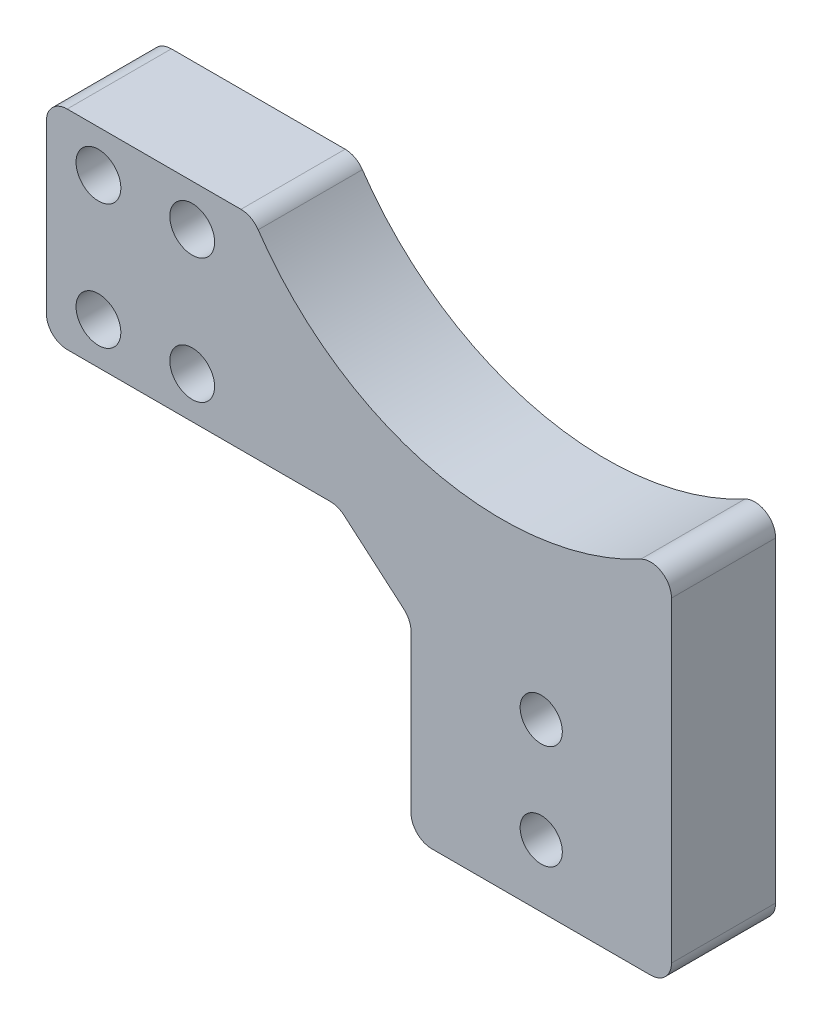
SolidWorks part; units mm, degrees
material "ABS"
ref_plane "前视基准面" through (0, 0, 0) normal (0, 0, 1) x (1, 0, 0)
ref_plane "上视基准面" through (0, 0, 0) normal (0, 1, 0) x (1, 0, 0)
ref_plane "右视基准面" through (0, 0, 0) normal (1, 0, 0) x (0, 0, -1)
other "Configuration Table"
sketch "草图1" plane through (0, 0, 0) normal (0, 0, 1) x (1, 0, 0)
  line L0 (0, 0) -> (0, -24)
  line L1 (0, -24) -> (25, -24)
  line L2 (25, -24) -> (25, 17.9268)
  line L3 (-15.2387, 26) -> (-35, 26)
  line L4 (-35, 26) -> (-35, 6)
  line L5 (-35, 6) -> (-7, 6)
  line L6 (-7, 6) -> (0, 0)
  arc A0 (25, 17.9268) -> (-15.2387, 26) centre (8.7, 41) cw
  dimension "D3" = 28.25
  dimension "D1" = 6
  dimension "D2" = 7
  dimension "D4" = 25
  dimension "D5" = 20
  dimension "D6" = 16.3
  dimension "D7" = 35
  dimension "D8" = 60
  dimension "D9" = 50
extrude "凸台-拉伸1" add sketch "草图1" along normal mid plane 10
fillet "圆角1" radius 2 6 edges at (-7, 6, 0) (-35, 6, 0) (25, -24, 0) (0, -24, 0) (0, 0, 0) (-35, 26, 0)
fillet "圆角2" radius 2 2 edges at (25, 17.9268, 0) (-15.2387, 26, 0)
sketch "草图2" plane through (0, 0, 5) normal (0, 0, 1) x (1, 0, 0)
  line L0 (-33, 6) -> (-7.7398, 6) construction
  line L1 (7.5, -12) -> (17.5, -12) construction
  line L2 (7.5, -12) -> (7.5, -2) construction
  line L3 (7.5, -2) -> (17.5, -2) construction
  line L4 (17.5, -12) -> (17.5, -2) construction
  line L5 (7.5, -12) -> (17.5, -2) construction
  line L6 (7.5, -2) -> (17.5, -12) construction
  line L7 (12.5, -7) -> (12.5, -24) construction
  line L8 (2, -24) -> (23, -24) construction
  circle A4 centre (12.5, -2) radius 2.025
  circle A5 centre (12.5, -12) radius 2.025
  point P0 (12.5, -7)
  dimension "D4" = 4.05
  dimension "D1" = 8
  dimension "D2" = 10
  dimension "D3" = 10
extrude "切除-拉伸1" cut sketch "草图2" against normal through all
sketch "草图3" plane through (0, 0, 5) normal (0, 0, 1) x (1, 0, 0)
  line L0 (0, -0.9199) -> (0, -22) construction
  line L1 (0, -18) -> (25, -18)
  line L2 (0, -18) -> (0, -24)
  line L3 (0, -24) -> (25, -24)
  line L4 (25, -18) -> (25, -24)
  line L5 (2, -24) -> (23, -24) construction
  line L6 (25, -22) -> (25, 14.3434) construction
  dimension "D1" = 6
extrude "切除-拉伸2" cut sketch "草图3" against normal through all
fillet "圆角3" radius 2 2 edges at (25, -18, 0) (0, -18, 0)
sketch "草图4" plane through (0, 0, 5) normal (0, 0, 1) x (1, 0, 0)
  line L0 (-35, 24) -> (-35, 8) construction
  line L1 (-16.3212, 26) -> (-33, 26) construction
  line L2 (-33, 6) -> (-7.7398, 6) construction
  circle A0 centre (-30, 22) radius 2.15
  circle A1 centre (-30, 10) radius 2.15
  dimension "D1" = 4.3
  dimension "D3" = 5
  dimension "D4" = 4
  dimension "D5" = 4
  dimension "D2" = 5
extrude "切除-拉伸3" cut sketch "草图4" against normal through all both and the other way through all
sketch "草图5" plane through (0, 0, 5) normal (0, 0, 1) x (1, 0, 0)
  line L1 (-30, 22) -> (-21, 22) construction
  line L2 (-30, 22) -> (-30, 10) construction
  line L3 (-30, 10) -> (-21, 10) construction
  line L4 (-21, 22) -> (-21, 10) construction
  circle A0 centre (-30, 10) radius 2.15 construction
  circle A1 centre (-21, 10) radius 2.15
  circle A2 centre (-21, 22) radius 2.15
  dimension "D2" = 4.3
  dimension "D1" = 9
extrude "切除-拉伸4" cut sketch "草图5" against normal through all both
